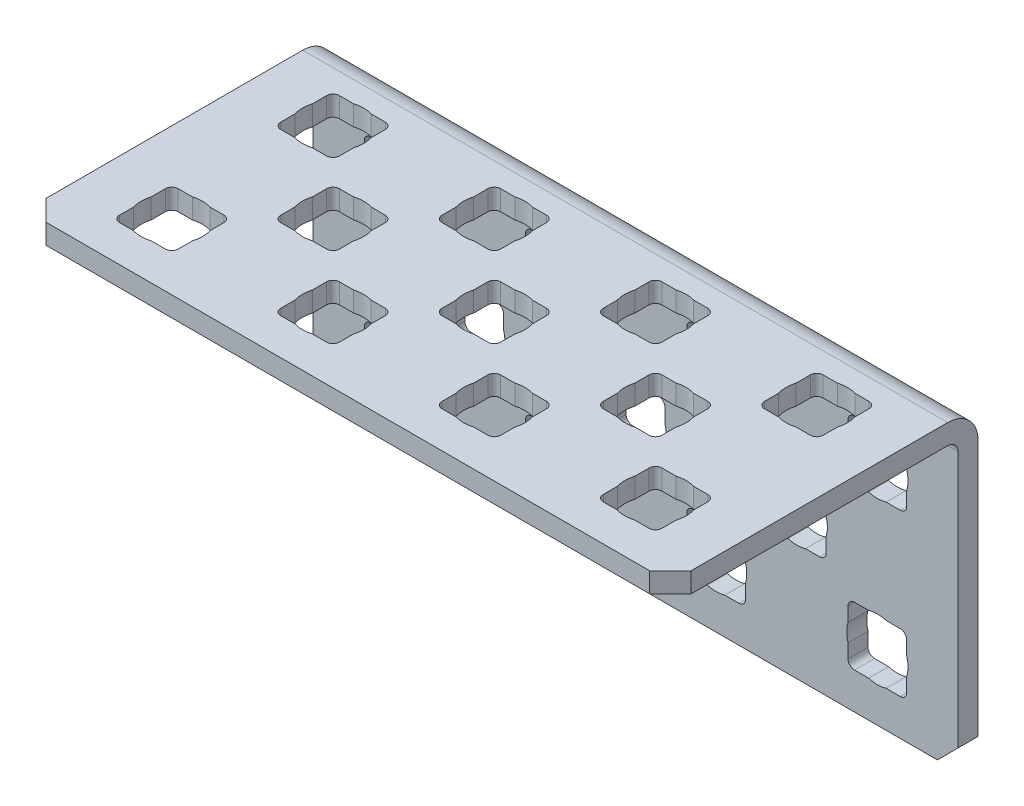
SolidWorks part; units mm, degrees
material "Custom Plastic"
ref_plane "Front Plane" through (0, 0, 0) normal (0, 0, 1) x (1, 0, 0)
ref_plane "Top Plane" through (0, 0, 0) normal (0, 1, 0) x (1, 0, 0)
ref_plane "Right Plane" through (0, 0, 0) normal (1, 0, 0) x (0, 0, -1)
ref_plane "Plane1" through (0, -12.1158, 0) normal (0, -1, 0) x (1, 0, 0)
sketch "Sketch1" plane through (0, -12.1158, 0) normal (0, -1, 0) x (1, 0, 0)
  line L0 (-25.4, 0) -> (25.4, 0)
  line L1 (25.4, 0) -> (25.4, 24.2316)
  line L2 (25.4, 24.2316) -> (-25.4, 24.2316)
  line L3 (-25.4, 24.2316) -> (-25.4, 0)
extrude "Boss-Extrude1" add sketch "Sketch1" against normal blind 24.2316
sketch "Sketch2" plane through (-25.4, 0, 0) normal (-1, 0, 0) x (0, 0, 1)
  line L0 (24.2316, 10.541) -> (1.5748, 10.541)
  line L1 (1.5748, 10.541) -> (1.5748, -12.1158)
  line L2 (1.5748, -12.1158) -> (24.2316, -12.1158)
  line L3 (24.2316, -12.1158) -> (24.2316, 10.541)
extrude "Cut-Extrude1" cut sketch "Sketch2" against normal through all
sketch "Sketch3" plane through (0, 12.1158, 0) normal (0, 1, 0) x (-1, 0, 0)
  line L0 (-16.7386, 8.6614) -> (-21.3614, 8.6614)
  line L1 (-21.3614, 8.6614) -> (-21.3614, 4.0386)
  line L2 (-21.3614, 4.0386) -> (-16.7386, 4.0386)
  line L3 (-16.7386, 4.0386) -> (-16.7386, 8.6614)
extrude "Cut-Extrude2" cut sketch "Sketch3" against normal through all
sketch "Sketch4" plane through (0, 12.1158, 0) normal (0, 1, 0) x (-1, 0, 0)
  line L0 (-4.0386, 8.6614) -> (-8.6614, 8.6614)
  line L1 (-8.6614, 8.6614) -> (-8.6614, 4.0386)
  line L2 (-8.6614, 4.0386) -> (-4.0386, 4.0386)
  line L3 (-4.0386, 4.0386) -> (-4.0386, 8.6614)
extrude "Cut-Extrude3" cut sketch "Sketch4" against normal through all
sketch "Sketch5" plane through (0, 12.1158, 0) normal (0, 1, 0) x (-1, 0, 0)
  line L0 (8.6614, 8.6614) -> (4.0386, 8.6614)
  line L1 (4.0386, 8.6614) -> (4.0386, 4.0386)
  line L2 (4.0386, 4.0386) -> (8.6614, 4.0386)
  line L3 (8.6614, 4.0386) -> (8.6614, 8.6614)
extrude "Cut-Extrude4" cut sketch "Sketch5" against normal through all
sketch "Sketch6" plane through (0, 12.1158, 0) normal (0, 1, 0) x (-1, 0, 0)
  line L0 (21.3614, 8.6614) -> (16.7386, 8.6614)
  line L1 (16.7386, 8.6614) -> (16.7386, 4.0386)
  line L2 (16.7386, 4.0386) -> (21.3614, 4.0386)
  line L3 (21.3614, 4.0386) -> (21.3614, 8.6614)
extrude "Cut-Extrude5" cut sketch "Sketch6" against normal through all
sketch "Sketch7" plane through (0, 12.1158, 0) normal (0, 1, 0) x (-1, 0, 0)
  line L0 (-10.3886, 15.0114) -> (-15.0114, 15.0114)
  line L1 (-15.0114, 15.0114) -> (-15.0114, 10.3886)
  line L2 (-15.0114, 10.3886) -> (-10.3886, 10.3886)
  line L3 (-10.3886, 10.3886) -> (-10.3886, 15.0114)
extrude "Cut-Extrude6" cut sketch "Sketch7" against normal through all
sketch "Sketch8" plane through (0, 12.1158, 0) normal (0, 1, 0) x (-1, 0, 0)
  line L0 (2.3114, 15.0114) -> (-2.3114, 15.0114)
  line L1 (-2.3114, 15.0114) -> (-2.3114, 10.3886)
  line L2 (-2.3114, 10.3886) -> (2.3114, 10.3886)
  line L3 (2.3114, 10.3886) -> (2.3114, 15.0114)
extrude "Cut-Extrude7" cut sketch "Sketch8" against normal through all
sketch "Sketch9" plane through (0, 12.1158, 0) normal (0, 1, 0) x (-1, 0, 0)
  line L0 (15.0114, 15.0114) -> (10.3886, 15.0114)
  line L1 (10.3886, 15.0114) -> (10.3886, 10.3886)
  line L2 (10.3886, 10.3886) -> (15.0114, 10.3886)
  line L3 (15.0114, 10.3886) -> (15.0114, 15.0114)
extrude "Cut-Extrude8" cut sketch "Sketch9" against normal through all
sketch "Sketch10" plane through (0, 12.1158, 0) normal (0, 1, 0) x (-1, 0, 0)
  line L0 (-16.7386, 21.3614) -> (-21.3614, 21.3614)
  line L1 (-21.3614, 21.3614) -> (-21.3614, 16.7386)
  line L2 (-21.3614, 16.7386) -> (-16.7386, 16.7386)
  line L3 (-16.7386, 16.7386) -> (-16.7386, 21.3614)
extrude "Cut-Extrude9" cut sketch "Sketch10" against normal through all
sketch "Sketch11" plane through (0, 12.1158, 0) normal (0, 1, 0) x (-1, 0, 0)
  line L0 (-4.0386, 21.3614) -> (-8.6614, 21.3614)
  line L1 (-8.6614, 21.3614) -> (-8.6614, 16.7386)
  line L2 (-8.6614, 16.7386) -> (-4.0386, 16.7386)
  line L3 (-4.0386, 16.7386) -> (-4.0386, 21.3614)
extrude "Cut-Extrude10" cut sketch "Sketch11" against normal through all
sketch "Sketch12" plane through (0, 12.1158, 0) normal (0, 1, 0) x (-1, 0, 0)
  line L0 (16.7386, 16.7386) -> (21.3614, 16.7386)
  line L1 (21.3614, 16.7386) -> (21.3614, 21.3614)
  line L2 (21.3614, 21.3614) -> (16.7386, 21.3614)
  line L3 (16.7386, 21.3614) -> (16.7386, 16.7386)
extrude "Cut-Extrude11" cut sketch "Sketch12" against normal through all
sketch "Sketch13" plane through (0, 0, 1.5748) normal (0, 0, 1) x (1, 0, 0)
  line L0 (21.3614, 3.4544) -> (21.3614, 8.0772)
  line L1 (21.3614, 8.0772) -> (16.7386, 8.0772)
  line L2 (16.7386, 8.0772) -> (16.7386, 3.4544)
  line L3 (16.7386, 3.4544) -> (21.3614, 3.4544)
extrude "Cut-Extrude12" cut sketch "Sketch13" against normal through all
sketch "Sketch14" plane through (0, 0, 1.5748) normal (0, 0, 1) x (1, 0, 0)
  line L0 (8.6614, 3.4544) -> (8.6614, 8.0772)
  line L1 (8.6614, 8.0772) -> (4.0386, 8.0772)
  line L2 (4.0386, 8.0772) -> (4.0386, 3.4544)
  line L3 (4.0386, 3.4544) -> (8.6614, 3.4544)
extrude "Cut-Extrude13" cut sketch "Sketch14" against normal through all
sketch "Sketch15" plane through (0, 0, 1.5748) normal (0, 0, 1) x (1, 0, 0)
  line L0 (-4.0386, 3.4544) -> (-4.0386, 8.0772)
  line L1 (-4.0386, 8.0772) -> (-8.6614, 8.0772)
  line L2 (-8.6614, 8.0772) -> (-8.6614, 3.4544)
  line L3 (-8.6614, 3.4544) -> (-4.0386, 3.4544)
extrude "Cut-Extrude14" cut sketch "Sketch15" against normal through all
sketch "Sketch16" plane through (0, 0, 1.5748) normal (0, 0, 1) x (1, 0, 0)
  line L0 (-16.7386, 3.4544) -> (-16.7386, 8.0772)
  line L1 (-16.7386, 8.0772) -> (-21.3614, 8.0772)
  line L2 (-21.3614, 8.0772) -> (-21.3614, 3.4544)
  line L3 (-21.3614, 3.4544) -> (-16.7386, 3.4544)
extrude "Cut-Extrude15" cut sketch "Sketch16" against normal through all
sketch "Sketch17" plane through (0, 0, 1.5748) normal (0, 0, 1) x (1, 0, 0)
  line L0 (15.0114, -2.8956) -> (15.0114, 1.7272)
  line L1 (15.0114, 1.7272) -> (10.3886, 1.7272)
  line L2 (10.3886, 1.7272) -> (10.3886, -2.8956)
  line L3 (10.3886, -2.8956) -> (15.0114, -2.8956)
extrude "Cut-Extrude16" cut sketch "Sketch17" against normal through all
sketch "Sketch18" plane through (0, 0, 1.5748) normal (0, 0, 1) x (1, 0, 0)
  line L0 (2.3114, -2.8956) -> (2.3114, 1.7272)
  line L1 (2.3114, 1.7272) -> (-2.3114, 1.7272)
  line L2 (-2.3114, 1.7272) -> (-2.3114, -2.8956)
  line L3 (-2.3114, -2.8956) -> (2.3114, -2.8956)
extrude "Cut-Extrude17" cut sketch "Sketch18" against normal through all
sketch "Sketch19" plane through (0, 0, 1.5748) normal (0, 0, 1) x (1, 0, 0)
  line L0 (-10.3886, -2.8956) -> (-10.3886, 1.7272)
  line L1 (-10.3886, 1.7272) -> (-15.0114, 1.7272)
  line L2 (-15.0114, 1.7272) -> (-15.0114, -2.8956)
  line L3 (-15.0114, -2.8956) -> (-10.3886, -2.8956)
extrude "Cut-Extrude18" cut sketch "Sketch19" against normal through all
sketch "Sketch20" plane through (0, 0, 1.5748) normal (0, 0, 1) x (1, 0, 0)
  line L0 (21.3614, -9.2456) -> (21.3614, -4.6228)
  line L1 (21.3614, -4.6228) -> (16.7386, -4.6228)
  line L2 (16.7386, -4.6228) -> (16.7386, -9.2456)
  line L3 (16.7386, -9.2456) -> (21.3614, -9.2456)
extrude "Cut-Extrude19" cut sketch "Sketch20" against normal through all
sketch "Sketch21" plane through (0, 0, 1.5748) normal (0, 0, 1) x (1, 0, 0)
  line L0 (8.6614, -9.2456) -> (8.6614, -4.6228)
  line L1 (8.6614, -4.6228) -> (4.0386, -4.6228)
  line L2 (4.0386, -4.6228) -> (4.0386, -9.2456)
  line L3 (4.0386, -9.2456) -> (8.6614, -9.2456)
extrude "Cut-Extrude20" cut sketch "Sketch21" against normal through all
sketch "Sketch22" plane through (0, 0, 1.5748) normal (0, 0, 1) x (1, 0, 0)
  line L0 (-16.7386, -9.2456) -> (-16.7386, -4.6228)
  line L1 (-16.7386, -4.6228) -> (-21.3614, -4.6228)
  line L2 (-21.3614, -4.6228) -> (-21.3614, -9.2456)
  line L3 (-21.3614, -9.2456) -> (-16.7386, -9.2456)
extrude "Cut-Extrude21" cut sketch "Sketch22" against normal through all
sketch "Sketch23" plane through (0, 0, 1.5748) normal (0, 0, 1) x (1, 0, 0)
  line L0 (-4.0386, -9.2456) -> (-4.0386, -4.6228)
  line L1 (-4.0386, -4.6228) -> (-8.6614, -4.6228)
  line L2 (-8.6614, -4.6228) -> (-8.6614, -9.2456)
  line L3 (-8.6614, -9.2456) -> (-4.0386, -9.2456)
extrude "Cut-Extrude22" cut sketch "Sketch23" against normal through all
sketch "Sketch24" plane through (0, 10.541, 0) normal (0, -1, 0) x (1, 0, 0)
  line L0 (-4.0386, 16.7386) -> (-4.0386, 21.3614)
  line L1 (-4.0386, 21.3614) -> (-8.6614, 21.3614)
  line L2 (-8.6614, 21.3614) -> (-8.6614, 16.7386)
  line L3 (-8.6614, 16.7386) -> (-4.0386, 16.7386)
extrude "Cut-Extrude23" cut sketch "Sketch24" against normal through all
chamfer "Chamfer1" distance 1.6256 angle 45 4 edges at (-25.4, 11.3284, 24.2316) (25.4, 11.3284, 24.2316) (25.4, -12.1158, 0.7874) (-25.4, -12.1158, 0.7874)
fillet "Fillet1" radius 0.508 88 edges at (-2.3114, 11.3284, 15.0114) (-21.3614, 11.3284, 21.3614) (4.0386, 11.3284, 8.6614) (-8.6614, -9.2456, 0.7874) (16.7386, 11.3284, 21.3614) (-4.0386, -9.2456, 0.7874) (-21.3614, 11.3284, 8.6614) (-21.3614, -4.6228, 0.7874) (-4.0386, -4.6228, 0.7874) (-16.7386, -4.6228, 0.7874) (4.0386, 11.3284, 21.3614) (-21.3614, -9.2456, 0.7874) (-15.0114, 11.3284, 15.0114) (-16.7386, -9.2456, 0.7874) (10.3886, 11.3284, 15.0114) (4.0386, -4.6228, 0.7874) (-8.6614, 11.3284, 8.6614) (8.6614, -4.6228, 0.7874) (16.7386, 11.3284, 8.6614) (4.0386, -9.2456, 0.7874) (-8.6614, 11.3284, 16.7386) (8.6614, -9.2456, 0.7874) (-21.3614, 11.3284, 16.7386) (16.7386, -4.6228, 0.7874) (4.0386, 11.3284, 16.7386) (21.3614, -4.6228, 0.7874) (16.7386, 11.3284, 16.7386) (16.7386, -9.2456, 0.7874) (-15.0114, 11.3284, 10.3886) (21.3614, -9.2456, 0.7874) (-2.3114, 11.3284, 10.3886) (-15.0114, 1.7272, 0.7874) (10.3886, 11.3284, 10.3886) (-10.3886, 1.7272, 0.7874) (-21.3614, 11.3284, 4.0386) (-15.0114, -2.8956, 0.7874) (-8.6614, 11.3284, 4.0386) (-10.3886, -2.8956, 0.7874) (4.0386, 11.3284, 4.0386) (-2.3114, 1.7272, 0.7874) (16.7386, 11.3284, 4.0386) (2.3114, 1.7272, 0.7874) (-4.0386, 11.3284, 21.3614) (-2.3114, -2.8956, 0.7874) (-4.0386, 11.3284, 16.7386) (2.3114, -2.8956, 0.7874) (-16.7386, 11.3284, 21.3614) (10.3886, 1.7272, 0.7874) (-16.7386, 11.3284, 16.7386) (15.0114, 1.7272, 0.7874) (8.6614, 11.3284, 21.3614) (10.3886, -2.8956, 0.7874) (8.6614, 11.3284, 16.7386) (15.0114, -2.8956, 0.7874) (21.3614, 11.3284, 21.3614) (-21.3614, 8.0772, 0.7874) (21.3614, 11.3284, 16.7386) (-16.7386, 8.0772, 0.7874) (-10.3886, 11.3284, 15.0114) (-21.3614, 3.4544, 0.7874) (-10.3886, 11.3284, 10.3886) (-16.7386, 3.4544, 0.7874) (2.3114, 11.3284, 15.0114) (-8.6614, 8.0772, 0.7874) (2.3114, 11.3284, 10.3886) (-4.0386, 8.0772, 0.7874) (15.0114, 11.3284, 15.0114) (-8.6614, 3.4544, 0.7874) (15.0114, 11.3284, 10.3886) (-4.0386, 3.4544, 0.7874) (-16.7386, 11.3284, 8.6614) (4.0386, 8.0772, 0.7874) (-16.7386, 11.3284, 4.0386) (8.6614, 8.0772, 0.7874) (-4.0386, 11.3284, 8.6614) (4.0386, 3.4544, 0.7874) (-4.0386, 11.3284, 4.0386) (8.6614, 3.4544, 0.7874) (8.6614, 11.3284, 8.6614) (16.7386, 8.0772, 0.7874) (8.6614, 11.3284, 4.0386) (21.3614, 8.0772, 0.7874) (21.3614, 11.3284, 8.6614) (21.3614, 3.4544, 0.7874) (21.3614, 11.3284, 4.0386) (-8.6614, -4.6228, 0.7874) (-8.6614, 11.3284, 21.3614) (16.7386, 3.4544, 0.7874)
fillet "Fillet2" radius 0.8128 1 edges at (0, 10.541, 1.5748)
fillet "Fillet3" radius 2.3876 1 edges at (0, 12.1158, 0)
sketch "Sketch25" plane through (0, 0, 0) normal (0, 0, -1) x (-1, 0, 0)
  line L0 (-21.3614, -6.9342) -> (-16.7386, -6.9342) construction
  line L1 (-21.3614, -8.7376) -> (-21.3614, -5.1308) construction
  line L2 (-16.7386, -5.1308) -> (-16.7386, -8.7376) construction
  circle A0 centre (-19.05, -6.9342) radius 2.413
  dimension "D1" = 4.826
extrude "Cut-Extrude24" cut sketch "Sketch25" against normal blind 2.54
pattern_linear "LPattern1" count 4 spacing 12.7 along (-1, 0, 0) count 2 spacing 12.7 along (0, 1, 0) of "Cut-Extrude24"
sketch "Sketch26" plane through (0, 0, 0) normal (0, 0, -1) x (-1, 0, 0)
  line L0 (-15.0114, -0.5842) -> (-10.3886, -0.5842) construction
  line L1 (-15.0114, -2.3876) -> (-15.0114, 1.2192) construction
  line L2 (-10.3886, 1.2192) -> (-10.3886, -2.3876) construction
  circle A0 centre (-12.7, -0.5842) radius 2.413
  dimension "D1" = 4.826
extrude "Cut-Extrude25" cut sketch "Sketch26" against normal blind 2.54
pattern_linear "LPattern2" count 3 spacing 12.7 along (-1, 0, 0) of "Cut-Extrude25"
sketch "Sketch27" plane through (0, 12.1158, 0) normal (0, 1, 0) x (1, 0, 0)
  line L0 (-21.3614, -19.05) -> (-16.7386, -19.05) construction
  line L1 (-21.3614, -17.2466) -> (-21.3614, -20.8534) construction
  line L2 (-16.7386, -20.8534) -> (-16.7386, -17.2466) construction
  circle A0 centre (-19.05, -19.05) radius 2.413
  dimension "D1" = 4.826
extrude "Cut-Extrude26" cut sketch "Sketch27" against normal blind 2.54
pattern_linear "LPattern3" count 4 spacing 12.7 along (1, 0, 0) count 2 spacing 12.7 along (0, 0, -1) of "Cut-Extrude26"
sketch "Sketch28" plane through (0, 12.1158, 0) normal (0, 1, 0) x (1, 0, 0)
  line L0 (-15.0114, -12.7) -> (-10.3886, -12.7) construction
  line L1 (-15.0114, -10.8966) -> (-15.0114, -14.5034) construction
  line L2 (-10.3886, -14.5034) -> (-10.3886, -10.8966) construction
  circle A0 centre (-12.7, -12.7) radius 2.413
  dimension "D1" = 4.826
extrude "Cut-Extrude27" cut sketch "Sketch28" against normal blind 2.54
pattern_linear "LPattern4" count 3 spacing 12.7 along (1, 0, 0) of "Cut-Extrude27"
